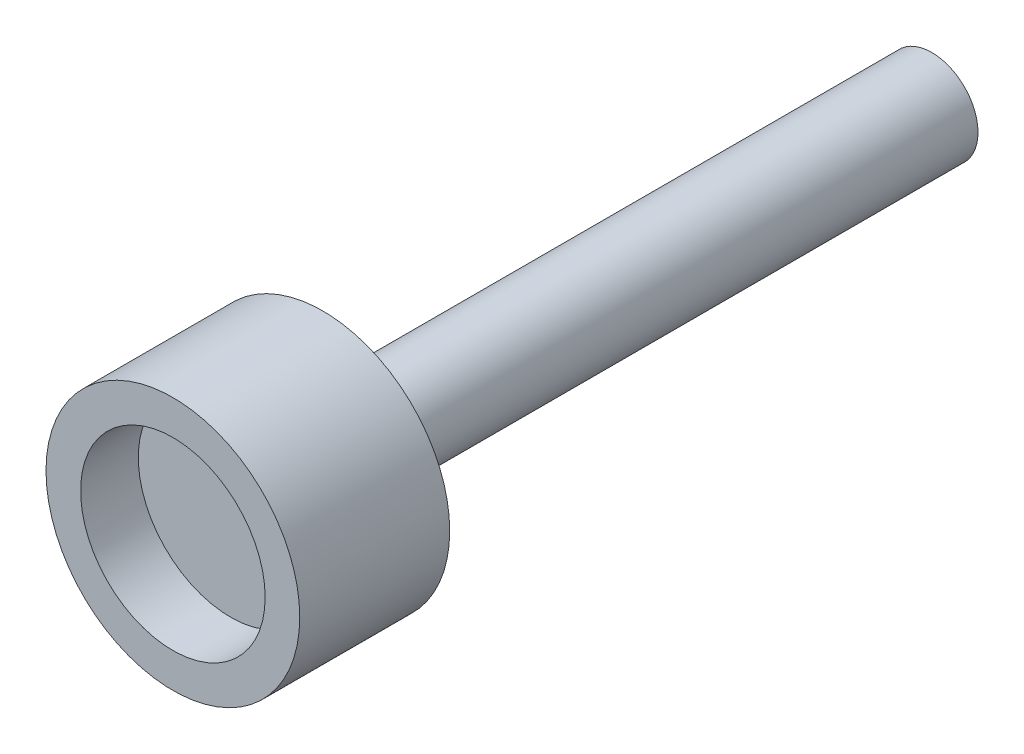
SolidWorks part; units mm, degrees
ref_plane "Alzado" through (0, 0, 0) normal (0, 0, 1) x (1, 0, 0)
ref_plane "Planta" through (0, 0, 0) normal (0, 1, 0) x (1, 0, 0)
ref_plane "Vista lateral" through (0, 0, 0) normal (1, 0, 0) x (0, 0, -1)
sketch "Croquis1" plane through (0, 0, 0) normal (0, 0, 1) x (1, 0, 0)
  circle A0 centre (0, 0) radius 11
  dimension "D1" = 22
extrude "Saliente-Extruir1" add sketch "Croquis1" along normal blind 13
sketch "Croquis2" plane through (0, 0, 13) normal (0, 0, 1) x (1, 0, 0)
  circle A0 centre (0, 0) radius 8
  dimension "D1" = 16
extrude "Cortar-Extruir1" cut sketch "Croquis2" against normal blind 5
sketch "Croquis3" plane through (0, 0, 0) normal (1, 0, 0) x (0, 0, -1)
  line L1 (-5, 0) -> (0, 0) construction
  line L2 (0, -11) -> (0, 11) construction
  circle A0 centre (-5, 0) radius 1.5
  dimension "D2" = 3
  dimension "D1" = 5
extrude "Cortar-Extruir2" cut sketch "Croquis3" against normal blind 15
sketch "Croquis4" plane through (0, 0, 0) normal (0, 0, -1) x (-1, 0, 0)
  circle A0 centre (0, 0) radius 4
  dimension "D1" = 8
extrude "Saliente-Extruir2" add sketch "Croquis4" along normal blind 52.8
